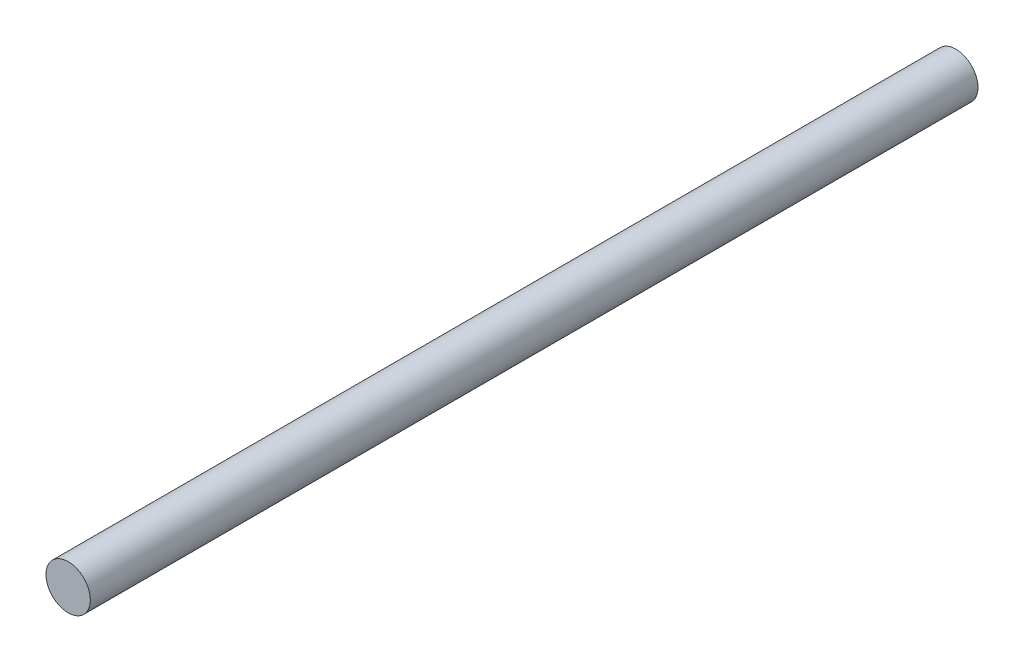
SolidWorks part; units mm, degrees
ref_plane "Plan de face" through (0, 0, 0) normal (0, 0, 1) x (1, 0, 0)
ref_plane "Plan de dessus" through (0, 0, 0) normal (0, 1, 0) x (1, 0, 0)
ref_plane "Plan de droite" through (0, 0, 0) normal (1, 0, 0) x (0, 0, -1)
sketch "Esquisse1" plane through (0, 0, 0) normal (0, 0, 1) x (1, 0, 0)
  circle A0 centre (0, 0) radius 0.5
  dimension "D1" = 1
extrude "Boss.-Extru.1" add sketch "Esquisse1" along normal blind 20
